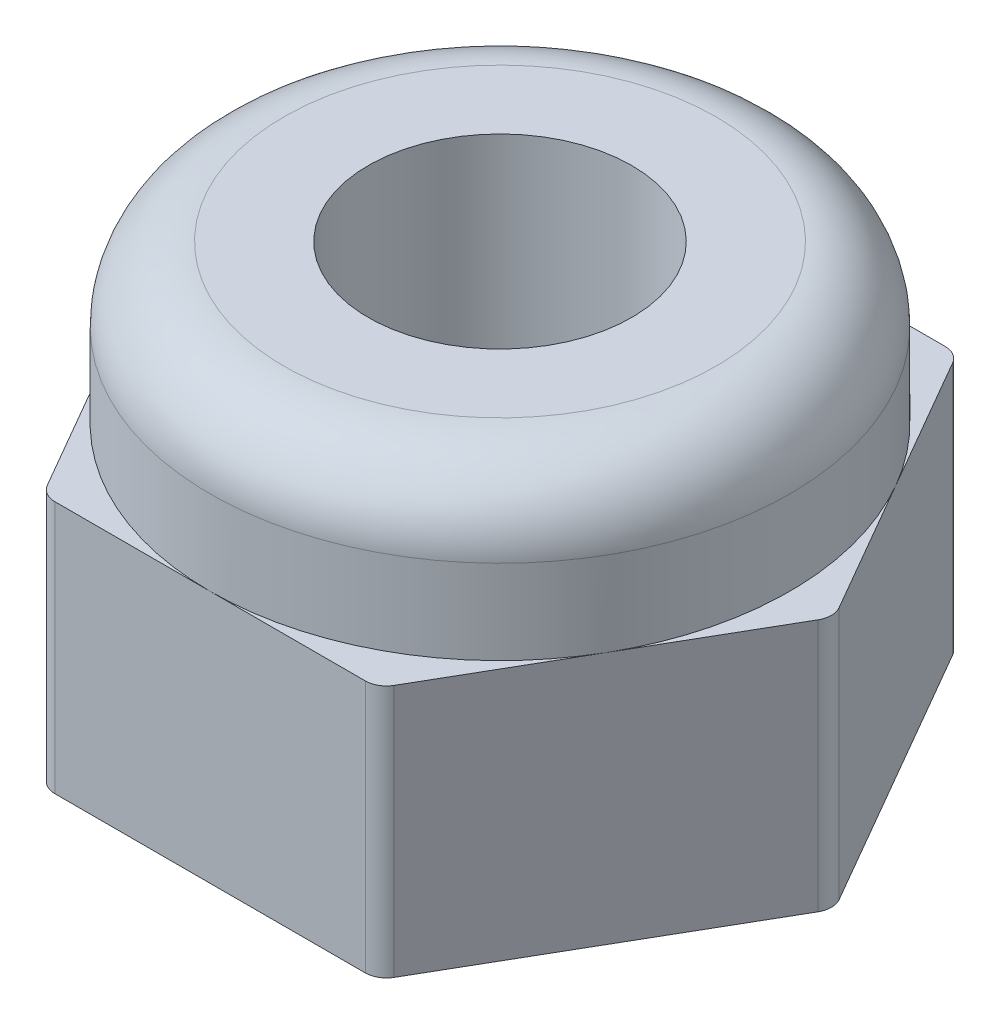
SolidWorks part; units mm, degrees
ref_plane "Front Plane" through (0, 0, 0) normal (0, 0, 1) x (1, 0, 0)
ref_plane "Top Plane" through (0, 0, 0) normal (0, 1, 0) x (1, 0, 0)
ref_plane "Right Plane" through (0, 0, 0) normal (1, 0, 0) x (0, 0, -1)
sketch "Sketch1" plane through (0, 0, 0) normal (0, 1, 0) x (1, 0, 0)
  line L1 (3.1754, 0) -> (1.5877, 2.75)
  line L2 (1.5877, 2.75) -> (-1.5877, 2.75)
  line L3 (-1.5877, 2.75) -> (-3.1754, 0)
  line L4 (-3.1754, 0) -> (-1.5877, -2.75)
  line L5 (-1.5877, -2.75) -> (1.5877, -2.75)
  line L6 (1.5877, -2.75) -> (3.1754, 0)
  circle A0 centre (0, 0) radius 2.75 construction
  dimension "D1" = 5.5
extrude "Boss-Extrude1" add sketch "Sketch1" along normal blind 2.4
sketch "Sketch2" plane through (0, 0, 0) normal (0, -1, 0) x (1, 0, 0)
  line L0 (-1.5877, 2.75) -> (1.5877, 2.75) construction
  circle A0 centre (0, 0) radius 2.75
extrude "Boss-Extrude2" add sketch "Sketch2" against normal blind 3.9
fillet "Fillet1" radius 0.7 1 edges at (0, 3.9, -2.75)
fillet "Fillet2" radius 0.2 6 edges at (-1.5877, 1.2, 2.75) (-3.1754, 1.2, 0) (-1.5877, 1.2, -2.75) (1.5877, 1.2, -2.75) (3.1754, 1.2, 0) (1.5877, 1.2, 2.75)
hole_wizard "M3 Tapped Hole1" positions "Sketch3" profile "Sketch5" tap size "M3" standard "GB" end condition through all
sketch "Sketch3" plane through (0, 0, 0) normal (0, -1, 0) x (-1, 0, 0)
  point P0 (0, 0)
sketch "Sketch5" plane through (0, 0, 0) normal (1, 0, 0) x (0, 0, -1)
  line L0 (0, 0) -> (0, 3.9)
  line L1 (0, 3.9) -> (1.25, 3.9)
  line L2 (1.25, 3.9) -> (1.25, 0)
  line L5 (1.25, 0) -> (0, 0)
  line L11 (0, -6.35) -> (0, 107.95) construction
  dimension "Thru Tap Drill Dia." = 2.5
  dimension "Thru Tap Drill Depth" = 3.9
cosmetic thread "Hole Thread1"
